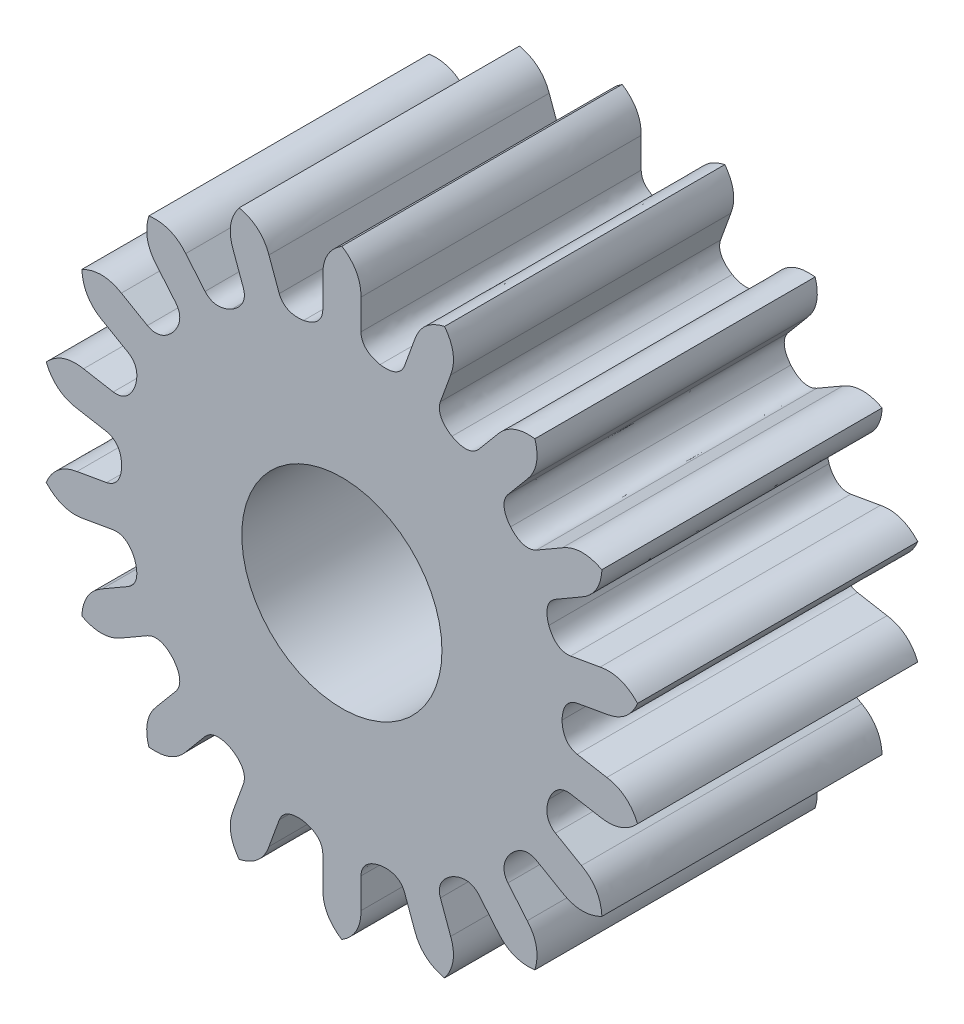
SolidWorks part; units mm, degrees
ref_plane "Alzado" through (0, 0, 0) normal (0, 0, 1) x (1, 0, 0)
ref_plane "Planta" through (0, 0, 0) normal (0, 1, 0) x (1, 0, 0)
ref_plane "Vista lateral" through (0, 0, 0) normal (1, 0, 0) x (0, 0, -1)
sketch "Sketch1" plane through (0, 0, 0) normal (0, 0, 1) x (1, 0, 0)
  line L0 (0, -1000) -> (0, 49000) construction
  line L1 (0, 0) -> (8682.4089, 49240.3877) construction
  line L2 (0, 0) -> (-8682.4089, 49240.3877) construction
  line L3 (-0.0037, -998.7287) -> (-0.0037, 49001.2713) construction
  line L4 (-1000.0625, 1.3781) -> (48999.9375, 1.3781) construction
  line L5 (-0.0037, 1.3781) -> (44997.0032, 21802.0515) construction
  line L6 (0.0954, -998.8135) -> (0.0954, 49001.1865) construction
  line L7 (0.0954, 1.3271) -> (0.0954, 1.1767)
  line L8 (0.0966, -998.9233) -> (0.0966, 49001.0767) construction
  line L9 (0.1496, -998.9123) -> (0.1496, 49001.0877) construction
  line L10 (-1000.023, 1.1326) -> (48999.977, 1.1326) construction
  line L11 (-1000.0185, 1.0914) -> (48999.9815, 1.0914) construction
  line L12 (-0.0954, 1.3271) -> (-0.0954, 1.1767)
  line L13 (0.3643, 1.2797) -> (0.3129, 1.1384)
  line L14 (0.5435, 1.2145) -> (0.4921, 1.0731)
  line L15 (0.78, 1.0779) -> (0.6833, 0.9627)
  line L16 (0.9261, 0.9553) -> (0.8294, 0.8401)
  line L17 (1.1016, 0.7461) -> (0.9714, 0.6709)
  line L18 (1.197, 0.581) -> (1.0667, 0.5058)
  line L19 (1.2904, 0.3244) -> (1.1423, 0.2982)
  line L20 (1.3235, 0.1366) -> (1.1754, 0.1104)
  line L21 (1.3235, -0.1366) -> (1.1754, -0.1104)
  line L22 (1.2904, -0.3244) -> (1.1423, -0.2982)
  line L23 (1.197, -0.581) -> (1.0667, -0.5058)
  line L24 (1.1016, -0.7461) -> (0.9714, -0.6709)
  line L25 (0.9261, -0.9553) -> (0.8294, -0.8401)
  line L26 (0.78, -1.0779) -> (0.6833, -0.9627)
  line L27 (0.5435, -1.2145) -> (0.4921, -1.0731)
  line L28 (0.3643, -1.2797) -> (0.3129, -1.1384)
  line L29 (0.0954, -1.3271) -> (0.0954, -1.1767)
  line L30 (-0.0954, -1.3271) -> (-0.0954, -1.1767)
  line L31 (-0.3643, -1.2797) -> (-0.3129, -1.1384)
  line L32 (-0.5435, -1.2145) -> (-0.4921, -1.0731)
  line L33 (-0.78, -1.0779) -> (-0.6833, -0.9627)
  line L34 (-0.9261, -0.9553) -> (-0.8294, -0.8401)
  line L35 (-1.1016, -0.7461) -> (-0.9714, -0.6709)
  line L36 (-1.197, -0.581) -> (-1.0667, -0.5058)
  line L37 (-1.2904, -0.3244) -> (-1.1423, -0.2982)
  line L38 (-1.3235, -0.1366) -> (-1.1754, -0.1104)
  line L39 (-1.3235, 0.1366) -> (-1.1754, 0.1104)
  line L40 (-1.2904, 0.3244) -> (-1.1423, 0.2982)
  line L41 (-1.197, 0.581) -> (-1.0667, 0.5058)
  line L42 (-1.1016, 0.7461) -> (-0.9714, 0.6709)
  line L43 (-0.9261, 0.9553) -> (-0.8294, 0.8401)
  line L44 (-0.78, 1.0779) -> (-0.6833, 0.9627)
  line L45 (-0.5435, 1.2145) -> (-0.4921, 1.0731)
  line L46 (-0.3643, 1.2797) -> (-0.3129, 1.1384)
  circle A0 centre (0, 0) radius 1.5 construction
  circle A1 centre (0, 0) radius 1.1 construction
  parabola Q0 (0, 1.4999) -> (0.0954, 1.3271) focus (-0.0037, 1.3781) apex (0.0765, 1.417)
  parabola Q1 (0, 1.4999) -> (-0.0954, 1.3271) focus (0.0037, 1.3781) apex (-0.0765, 1.417)
  parabola Q2 (0.513, 1.4095) -> (0.3643, 1.2797) focus (0.4749, 1.2937) apex (0.4127, 1.3577)
  parabola Q3 (0.513, 1.4095) -> (0.5435, 1.2145) focus (0.4678, 1.2963) apex (0.5565, 1.3054)
  parabola Q4 (0.9641, 1.149) -> (0.78, 1.0779) focus (0.8887, 1.0533) apex (0.8522, 1.1347)
  parabola Q5 (0.9641, 1.149) -> (0.9261, 0.9553) focus (0.883, 1.0581) apex (0.9694, 1.0363)
  parabola Q6 (1.299, 0.75) -> (1.1016, 0.7461) focus (1.1953, 0.6858) apex (1.1889, 0.7748)
  parabola Q7 (1.299, 0.75) -> (1.197, 0.581) focus (1.1916, 0.6923) apex (1.2654, 0.6422)
  parabola Q8 (1.4772, 0.2605) -> (1.2904, 0.3244) focus (1.3578, 0.2356) apex (1.3822, 0.3214)
  parabola Q9 (1.4772, 0.2605) -> (1.3235, 0.1366) focus (1.3565, 0.243) apex (1.4088, 0.1707)
  parabola Q10 (1.4772, -0.2605) -> (1.3235, -0.1366) focus (1.3565, -0.243) apex (1.4088, -0.1707)
  parabola Q11 (1.4772, -0.2605) -> (1.2904, -0.3244) focus (1.3578, -0.2356) apex (1.3822, -0.3214)
  parabola Q12 (1.299, -0.75) -> (1.197, -0.581) focus (1.1916, -0.6923) apex (1.2654, -0.6422)
  parabola Q13 (1.299, -0.75) -> (1.1016, -0.7461) focus (1.1953, -0.6858) apex (1.1889, -0.7748)
  parabola Q14 (0.9641, -1.149) -> (0.9261, -0.9553) focus (0.883, -1.0581) apex (0.9694, -1.0363)
  parabola Q15 (0.9641, -1.149) -> (0.78, -1.0779) focus (0.8887, -1.0533) apex (0.8522, -1.1347)
  parabola Q16 (0.513, -1.4095) -> (0.5435, -1.2145) focus (0.4678, -1.2963) apex (0.5565, -1.3054)
  parabola Q17 (0.513, -1.4095) -> (0.3643, -1.2797) focus (0.4749, -1.2937) apex (0.4127, -1.3577)
  parabola Q18 (0, -1.4999) -> (0.0954, -1.3271) focus (-0.0037, -1.3781) apex (0.0765, -1.417)
  parabola Q19 (0, -1.4999) -> (-0.0954, -1.3271) focus (0.0037, -1.3781) apex (-0.0765, -1.417)
  parabola Q20 (-0.513, -1.4095) -> (-0.3643, -1.2797) focus (-0.4749, -1.2937) apex (-0.4127, -1.3577)
  parabola Q21 (-0.513, -1.4095) -> (-0.5435, -1.2145) focus (-0.4678, -1.2963) apex (-0.5565, -1.3054)
  parabola Q22 (-0.9641, -1.149) -> (-0.78, -1.0779) focus (-0.8887, -1.0533) apex (-0.8522, -1.1347)
  parabola Q23 (-0.9641, -1.149) -> (-0.9261, -0.9553) focus (-0.883, -1.0581) apex (-0.9694, -1.0363)
  parabola Q24 (-1.299, -0.75) -> (-1.1016, -0.7461) focus (-1.1953, -0.6858) apex (-1.1889, -0.7748)
  parabola Q25 (-1.299, -0.75) -> (-1.197, -0.581) focus (-1.1916, -0.6923) apex (-1.2654, -0.6422)
  parabola Q26 (-1.4772, -0.2605) -> (-1.2904, -0.3244) focus (-1.3578, -0.2356) apex (-1.3822, -0.3214)
  parabola Q27 (-1.4772, -0.2605) -> (-1.3235, -0.1366) focus (-1.3565, -0.243) apex (-1.4088, -0.1707)
  parabola Q28 (-1.4772, 0.2605) -> (-1.3235, 0.1366) focus (-1.3565, 0.243) apex (-1.4088, 0.1707)
  parabola Q29 (-1.4772, 0.2605) -> (-1.2904, 0.3244) focus (-1.3578, 0.2356) apex (-1.3822, 0.3214)
  parabola Q30 (-1.299, 0.75) -> (-1.197, 0.581) focus (-1.1916, 0.6923) apex (-1.2654, 0.6422)
  parabola Q31 (-1.299, 0.75) -> (-1.1016, 0.7461) focus (-1.1953, 0.6858) apex (-1.1889, 0.7748)
  parabola Q32 (-0.9641, 1.149) -> (-0.9261, 0.9553) focus (-0.883, 1.0581) apex (-0.9694, 1.0363)
  parabola Q33 (-0.9641, 1.149) -> (-0.78, 1.0779) focus (-0.8887, 1.0533) apex (-0.8522, 1.1347)
  parabola Q34 (-0.513, 1.4095) -> (-0.5435, 1.2145) focus (-0.4678, 1.2963) apex (-0.5565, 1.3054)
  parabola Q35 (-0.513, 1.4095) -> (-0.3643, 1.2797) focus (-0.4749, 1.2937) apex (-0.4127, 1.3577)
  spline S0 degree 3 poles (0.0954, 1.1767) (0.0969, 1.1217) (0.1394, 1.0934) (0.191, 1.0833) knots 0 0 0 0 1 1 1 1
  spline S1 degree 3 poles (-0.0954, 1.1767) (-0.0969, 1.1217) (-0.1394, 1.0934) (-0.191, 1.0833) knots 0 0 0 0 1 1 1 1
  spline S2 degree 3 poles (0.3129, 1.1384) (0.2926, 1.0872) (0.2429, 1.0752) (0.191, 1.0833) knots 0 0 0 0 1 1 1 1
  spline S3 degree 3 poles (0.4921, 1.0731) (0.4747, 1.0209) (0.505, 0.9798) (0.55, 0.9526) knots 0 0 0 0 1 1 1 1
  spline S4 degree 3 poles (0.6833, 0.9627) (0.6468, 0.9216) (0.596, 0.9272) (0.55, 0.9526) knots 0 0 0 0 1 1 1 1
  spline S5 degree 3 poles (0.8294, 0.8401) (0.7952, 0.797) (0.8097, 0.748) (0.8426, 0.7071) knots 0 0 0 0 1 1 1 1
  spline S6 degree 3 poles (0.9714, 0.6709) (0.923, 0.6448) (0.8772, 0.6675) (0.8426, 0.7071) knots 0 0 0 0 1 1 1 1
  spline S7 degree 3 poles (1.0667, 0.5058) (1.0199, 0.4769) (1.0167, 0.4259) (1.0337, 0.3762) knots 0 0 0 0 1 1 1 1
  spline S8 degree 3 poles (1.1423, 0.2982) (1.0878, 0.2902) (1.0526, 0.3272) (1.0337, 0.3762) knots 0 0 0 0 1 1 1 1
  spline S9 degree 3 poles (1.1754, 0.1104) (1.1215, 0.0994) (1.101, 0.0525) (1.1, 0) knots 0 0 0 0 1 1 1 1
  spline S10 degree 3 poles (1.1754, -0.1104) (1.1215, -0.0994) (1.101, -0.0525) (1.1, 0) knots 0 0 0 0 1 1 1 1
  spline S11 degree 3 poles (1.1423, -0.2982) (1.0878, -0.2902) (1.0526, -0.3272) (1.0337, -0.3762) knots 0 0 0 0 1 1 1 1
  spline S12 degree 3 poles (1.0667, -0.5058) (1.0199, -0.4769) (1.0167, -0.4259) (1.0337, -0.3762) knots 0 0 0 0 1 1 1 1
  spline S13 degree 3 poles (0.9714, -0.6709) (0.923, -0.6448) (0.8772, -0.6675) (0.8426, -0.7071) knots 0 0 0 0 1 1 1 1
  spline S14 degree 3 poles (0.8294, -0.8401) (0.7952, -0.797) (0.8097, -0.748) (0.8426, -0.7071) knots 0 0 0 0 1 1 1 1
  spline S15 degree 3 poles (0.6833, -0.9627) (0.6468, -0.9216) (0.596, -0.9272) (0.55, -0.9526) knots 0 0 0 0 1 1 1 1
  spline S16 degree 3 poles (0.4921, -1.0731) (0.4747, -1.0209) (0.505, -0.9798) (0.55, -0.9526) knots 0 0 0 0 1 1 1 1
  spline S17 degree 3 poles (0.3129, -1.1384) (0.2926, -1.0872) (0.2429, -1.0752) (0.191, -1.0833) knots 0 0 0 0 1 1 1 1
  spline S18 degree 3 poles (0.0954, -1.1767) (0.0969, -1.1217) (0.1394, -1.0934) (0.191, -1.0833) knots 0 0 0 0 1 1 1 1
  spline S19 degree 3 poles (-0.0953, -1.1767) (-0.0969, -1.1217) (-0.1394, -1.0934) (-0.191, -1.0833) knots 0 0 0 0 1 1 1 1
  spline S20 degree 3 poles (-0.3129, -1.1384) (-0.2926, -1.0872) (-0.2429, -1.0752) (-0.191, -1.0833) knots 0 0 0 0 1 1 1 1
  spline S21 degree 3 poles (-0.4921, -1.0731) (-0.4747, -1.0209) (-0.505, -0.9798) (-0.55, -0.9526) knots 0 0 0 0 1 1 1 1
  spline S22 degree 3 poles (-0.6833, -0.9627) (-0.6468, -0.9216) (-0.596, -0.9272) (-0.55, -0.9526) knots 0 0 0 0 1 1 1 1
  spline S23 degree 3 poles (-0.8294, -0.8401) (-0.7952, -0.797) (-0.8097, -0.748) (-0.8426, -0.7071) knots 0 0 0 0 1 1 1 1
  spline S24 degree 3 poles (-0.9714, -0.6709) (-0.923, -0.6448) (-0.8772, -0.6675) (-0.8426, -0.7071) knots 0 0 0 0 1 1 1 1
  spline S25 degree 3 poles (-1.0667, -0.5058) (-1.0199, -0.4769) (-1.0167, -0.4259) (-1.0337, -0.3762) knots 0 0 0 0 1 1 1 1
  spline S26 degree 3 poles (-1.1423, -0.2982) (-1.0878, -0.2902) (-1.0526, -0.3272) (-1.0337, -0.3762) knots 0 0 0 0 1 1 1 1
  spline S27 degree 3 poles (-1.1754, -0.1104) (-1.1215, -0.0994) (-1.101, -0.0525) (-1.1, 0) knots 0 0 0 0 1 1 1 1
  spline S28 degree 3 poles (-1.1754, 0.1104) (-1.1215, 0.0994) (-1.101, 0.0525) (-1.1, 0) knots 0 0 0 0 1 1 1 1
  spline S29 degree 3 poles (-1.1423, 0.2982) (-1.0878, 0.2902) (-1.0526, 0.3272) (-1.0337, 0.3762) knots 0 0 0 0 1 1 1 1
  spline S30 degree 3 poles (-1.0667, 0.5058) (-1.0199, 0.4769) (-1.0167, 0.4259) (-1.0337, 0.3762) knots 0 0 0 0 1 1 1 1
  spline S31 degree 3 poles (-0.9714, 0.6709) (-0.923, 0.6448) (-0.8772, 0.6675) (-0.8426, 0.7071) knots 0 0 0 0 1 1 1 1
  spline S32 degree 3 poles (-0.8294, 0.8401) (-0.7952, 0.797) (-0.8097, 0.748) (-0.8426, 0.7071) knots 0 0 0 0 1 1 1 1
  spline S33 degree 3 poles (-0.6833, 0.9627) (-0.6468, 0.9216) (-0.596, 0.9272) (-0.55, 0.9526) knots 0 0 0 0 1 1 1 1
  spline S34 degree 3 poles (-0.4921, 1.0731) (-0.4747, 1.0209) (-0.505, 0.9798) (-0.55, 0.9526) knots 0 0 0 0 1 1 1 1
  spline S35 degree 3 poles (-0.3129, 1.1384) (-0.2926, 1.0872) (-0.2429, 1.0752) (-0.191, 1.0833) knots 0 0 0 0 1 1 1 1
  point P13 (0, 1.5)
  point P15 (-0.0037, 1.3781)
  point P18 (0.0765, 1.417)
  point P23 (0.191, 1.0833)
  point P34 (0.1496, 1.0914)
  point P36 (0.0966, 1.1326)
  point P233 (0, 0)
  dimension "D1" = 3
  dimension "D2" = 2.2
  dimension "D3" = 10
  dimension "D4" = 10
  dimension "D5" = 0.0037
  dimension "D6" = 25.85
  dimension "D7" = 0.0892
  dimension "D8" = 0.1219
  dimension "D9" = 0.0954
  dimension "D10" = 0.1504
  dimension "D11" = 0.0966
  dimension "D12" = 0.1496
  dimension "D13" = 1.1326
  dimension "D14" = 1.0914
  dimension "D15" = 18
extrude "Boss-Extrude1 (18 teeth)" add sketch "Sketch1" along normal blind 1.4
sketch "Sketch2" plane through (0, 0, 0) normal (0, 0, 1) x (1, 0, 0)
  circle A0 centre (0, 0) radius 0.5
  dimension "D1" = 1
extrude "Cut-Extrude1" cut sketch "Sketch2" along normal up to next
